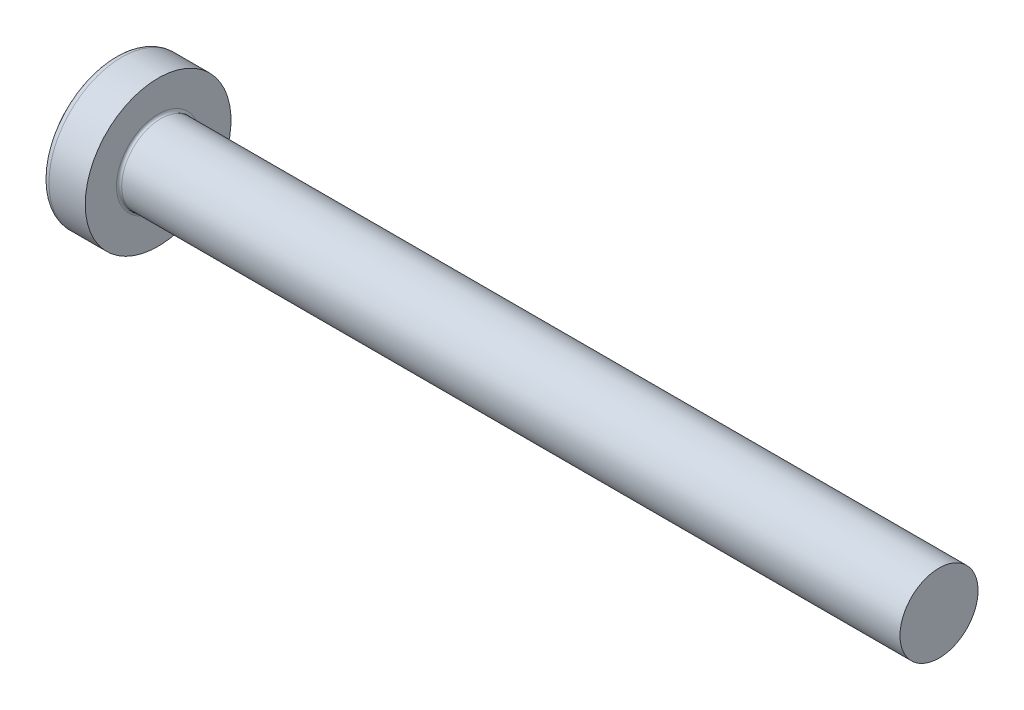
SolidWorks part; units mm, degrees
ref_plane "Plane1" through (0, 0, 0) normal (0, 0, 1) x (1, 0, 0)
ref_plane "Plane2" through (0, 0, 0) normal (0, 1, 0) x (1, 0, 0)
ref_plane "Plane3" through (0, 0, 0) normal (1, 0, 0) x (0, 0, -1)
sketch "BodySke" plane through (0, 0, 0) normal (0, 0, 1) x (1, 0, 0)
  line L0 (2.4, 1.5) -> (2.4, 2.8)
  line L1 (2.65, 6.35) -> (2.65, -3.175) construction
  line L2 (-25.4, 0) -> (127, 0) construction
  line L3 (32.4, 0) -> (0, 0)
  line L4 (2.4, 1.5) -> (32.4, 1.5)
  line L5 (32.4, 1.5) -> (32.4, 0)
  line L6 (1.0035, 2.8) -> (2.4, 2.8)
  line L8 (7.4, 6.35) -> (7.4, -3.175) construction
  arc A0 (0.7754, 2.6744) -> (0, 0) centre (5, 0) ccw
  arc A2 (0.7754, 2.6744) -> (1.0035, 2.8) centre (1.0035, 2.53) cw
  dimension "Head_fillet_rad" = 0.27
  dimension "Head_crown_rad" = 5
  dimension "Head_ht" = 2.4
  dimension "Diameter" = 3
  dimension "Length" = 30
  dimension "Head_dia" = 5.6
  dimension "Advance" = 0.5
  dimension "Thread_nom" = 25
revolve "Base-Revolve" add sketch "BodySke"
cosmetic thread "ThreadCosmetic" [suppressed]
fillet "Fillet1" radius 0.1 1 edges at (2.4, 0, 1.5)
sketch "Sketch3" plane through (0, 0, 0) normal (1, 0, 0) x (0, 0, -1)
  line L0 (0.37, -1.4) -> (-0.37, -1.4)
  line L1 (0.37, -1.4) -> (0.37, 1.4)
  line L2 (-0.37, 1.4) -> (0.37, 1.4)
  line L3 (-0.37, 1.4) -> (-0.37, -1.4)
  dimension "D1" = 1.4
  dimension "Cross_dia" = 2.8
  dimension "D2" = 0.37
  dimension "Cross_width" = 0.74
ref_plane "Plane4" through (1.75, 0, 0) normal (1, 0, 0) x (0, 0, -1)
sketch "Sketch4" plane through (1.75, 0, 0) normal (1, 0, 0) x (0, 0, -1)
  line L0 (0.37, -0.5275) -> (-0.37, -0.5275)
  line L1 (0.37, -0.5275) -> (0.37, 0.5275)
  line L2 (-0.37, 0.5275) -> (0.37, 0.5275)
  line L3 (-0.37, 0.5275) -> (-0.37, -0.5275)
  dimension "D1" = 0.74
  dimension "D2" = 1.055
  dimension "D3" = 0.37
  dimension "D4" = 0.5275
loft "Recess" cut profiles "Sketch3", "Sketch4"
pattern_circular "RecPat" count 2 every 90 about axis through (0, 0, 0) along (1, 0, 0) of "Recess"
sketch "RecCorSke" plane through (0, 0, 0) normal (0, 0, 1) x (1, 0, 0)
  line L0 (-3.175, 0) -> (15.875, 0) construction
  line L1 (-25.4, 0) -> (127, 0) construction
  line L2 (0, 0) -> (0, 0.6784)
  line L3 (0, 0.6784) -> (1.75, 0.556)
  line L4 (1.75, 0.556) -> (1.9307, 0)
  line L5 (1.9307, 0) -> (0, 0)
  dimension "Diameter" = 1.112
  dimension "Depth" = 1.75
  dimension "Draft_angle" = 4
  dimension "Bottom_angle" = 18
revolve "RecessCore" cut sketch "RecCorSke" angle 360 about L0
sketch "ThdSchSke" plane through (0, 0, 0) normal (0, 0, 1) x (1, 0, 0)
  line L0 (7.4, -1.2195) -> (7.2036, -1.5)
  line L1 (7.4, -1.2195) -> (7.5964, -1.5)
  line L2 (7.5964, -1.5) -> (7.5964, -1.875)
  line L3 (-3.175, 0) -> (5.1513, 0) construction
  line L5 (7.5964, -1.875) -> (7.2036, -1.875)
  line L6 (7.2036, -1.875) -> (7.2036, -1.5)
  dimension "Thread_minor" = 2.439
  dimension "Diameter" = 3
  dimension "Start" = 7.4
  dimension "SideAngle" = 55
  dimension "VeeAngle" = 70
  dimension "Overcut" = 3.75
revolve "ThreadSchematic" [suppressed] cut sketch "ThdSchSke" angle 360 about L3
pattern_linear "ThdSchPat" [suppressed]
equation "\"D1@Sketch3\" = \"Cross_dia@Sketch3\" / 2"
equation "\"D2@Sketch3\" = \"Cross_width@Sketch3\" / 2"
equation "\"Depth@RecCorSke\" = \"Cross_depth@Plane4\""
equation "\"D1@Sketch4\" = \"Cross_width@Sketch3\""
equation "\"D2@Sketch4\" = \"Cross_dia@Sketch3\" - 2.0 * \"Cross_depth@Plane4\" * tan(26.5  * 0.017453292)"
equation "\"D3@Sketch4\" = \"D1@Sketch4\" / 2"
equation "\"D4@Sketch4\" = \"D2@Sketch4\" / 2"
equation "\"Thread_length@ThreadCosmetic\" = ((sgn( (\"Length@BodySke\" - \"Advance@BodySke\" * 2.0 ) - \"Thread_nom@BodySke\" )-1)*( (\"Length@BodySke\" - \"Advance@BodySke\" * 2.0 ) - \"Thread_nom@BodySke\" ))/-2+ \"Thread_nom@BodySke\""
equation "\"Thread_minor@ThdSchSke\" = \"Thread_minor@ThreadCosmetic\""
equation "\"Diameter@ThdSchSke\" = \"Diameter@BodySke\""
equation "\"Overcut@ThdSchSke\" = \"Diameter@BodySke\" * 1.25"
equation "\"Start@ThdSchSke\" = \"Head_ht@BodySke\" + \"Length@BodySke\" - \"Thread_length@ThreadCosmetic\"  '---Non-countersunk---"
equation "\"Num_threads@ThdSchPat\" = int( \"Thread_length@ThreadCosmetic\" / \"Advance@BodySke\" + 0.999 )  + 1"
equation "\"Advance@ThdSchPat\" = \"Thread_length@ThreadCosmetic\" /  (\"Num_threads@ThdSchPat\" - 1) 'relax it"
